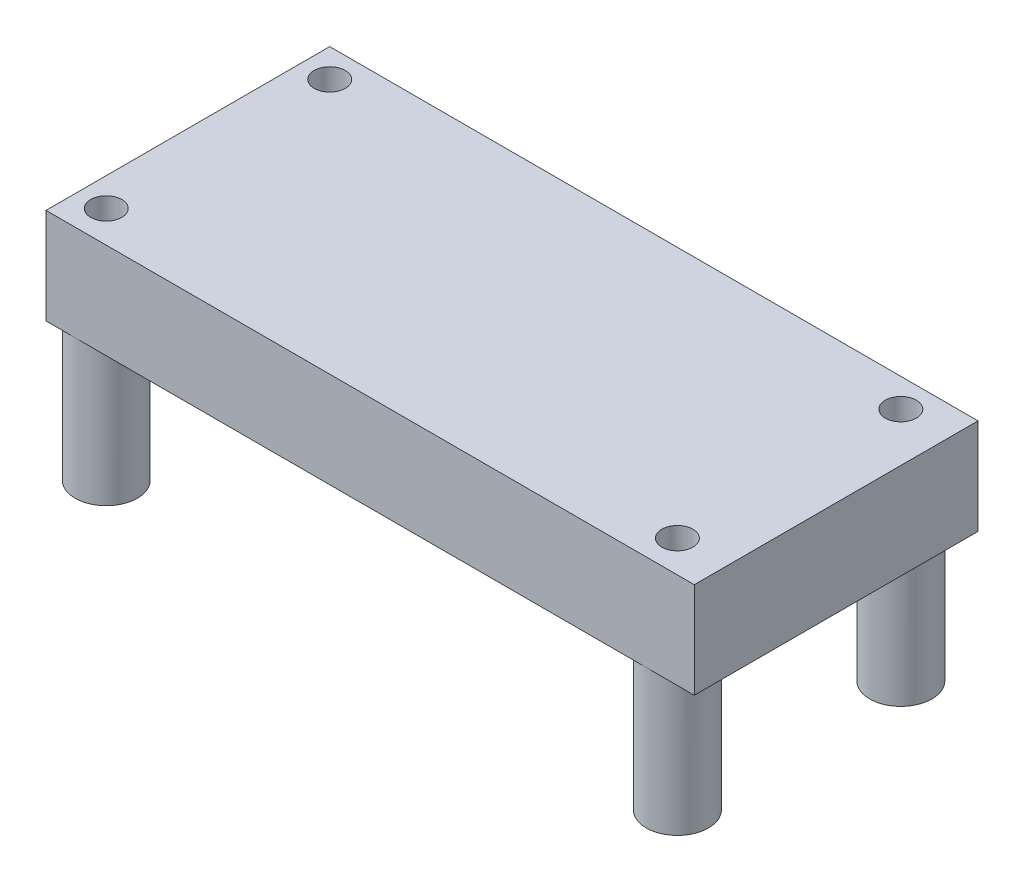
SolidWorks part; units mm, degrees
ref_plane "Front Plane" through (0, 0, 0) normal (0, 0, 1) x (1, 0, 0)
ref_plane "Top Plane" through (0, 0, 0) normal (0, 1, 0) x (1, 0, 0)
ref_plane "Right Plane" through (0, 0, 0) normal (1, 0, 0) x (0, 0, -1)
sketch "Sketch1" plane through (0, 0, 0) normal (0, 1, 0) x (1, 0, 0)
  line L1 (-16.8639, 11.4761) -> (35.2361, 11.4761)
  line L2 (-16.8639, 11.4761) -> (-16.8639, -11.3239)
  line L3 (-16.8639, -11.3239) -> (35.2361, -11.3239)
  line L4 (35.2361, 11.4761) -> (35.2361, -11.3239)
  dimension "D1" = 22.8
  dimension "D2" = 52.1
extrude "Boss-Extrude1" add sketch "Sketch1" along normal blind 7.6962
sketch "Sketch2" plane through (0, 0, 0) normal (0, -1, 0) x (1, 0, 0)
  circle A0 centre (-14.5779, 8.7677) radius 2.5
  circle A1 centre (31.3199, 8.7677) radius 2.5
  circle A2 centre (31.3199, -9.1901) radius 2.5
  circle A3 centre (-14.5779, -9.1901) radius 2.5
  dimension "D1" = 5
  dimension "D3" = 45.8978
  dimension "D6" = 5
  dimension "D9" = 5
  dimension "D12" = 5
  dimension "D2" = 17.9578
extrude "Boss-Extrude2" add sketch "Sketch2" along normal blind 11.2268
sketch "Sketch3" plane through (0, -11.2268, 0) normal (0, -1, 0) x (1, 0, 0)
  circle A0 centre (-14.5779, 8.7677) radius 1.25
  circle A1 centre (-14.5779, -9.1901) radius 1.25
  circle A2 centre (31.3199, -9.1901) radius 1.25
  circle A3 centre (31.3199, 8.7677) radius 1.25
  dimension "D1" = 2.5
  dimension "D2" = 2.5
  dimension "D3" = 2.5
  dimension "D4" = 2.5
extrude "Cut-Extrude1" cut sketch "Sketch3" against normal through all
